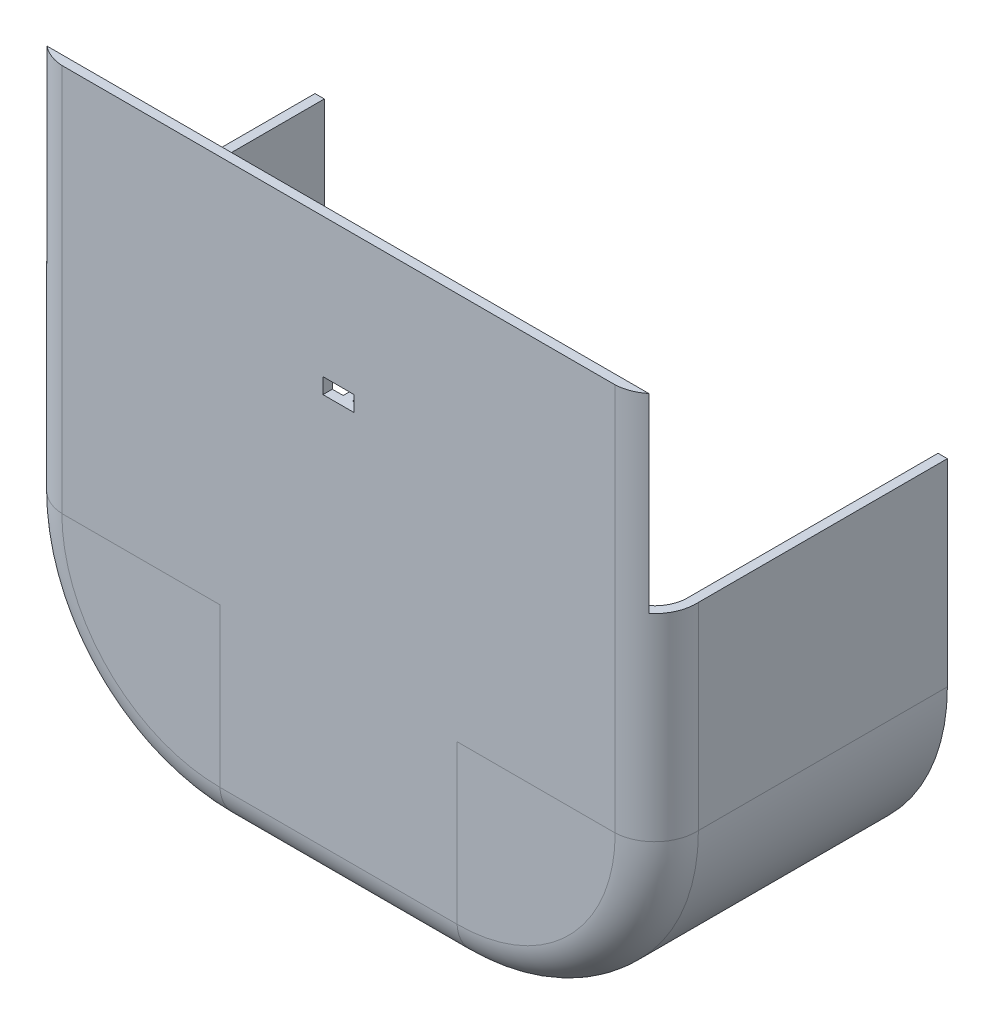
SolidWorks part; units mm, degrees
material "ABS"
ref_plane "Front Plane" through (0, 0, 0) normal (0, 0, 1) x (1, 0, 0)
ref_plane "Top Plane" through (0, 0, 0) normal (0, 1, 0) x (1, 0, 0)
ref_plane "Right Plane" through (0, 0, 0) normal (1, 0, 0) x (0, 0, -1)
sketch "Sketch1" plane through (0, 0, 0) normal (0, 0, 1) x (1, 0, 0)
  line L0 (-98.6, 98.6) -> (-98.6, -38.1)
  line L1 (-101.6, 101.6) -> (-101.6, -38.1)
  line L2 (-101.6, 101.6) -> (101.6, 101.6)
  line L3 (101.6, 101.6) -> (101.6, -38.1)
  line L4 (-38.1, -101.6) -> (38.1, -101.6)
  line L5 (-98.6, 98.6) -> (98.6, 98.6)
  line L6 (98.6, 98.6) -> (98.6, -38.1)
  line L7 (-38.1, -98.6) -> (38.1, -98.6)
  arc A0 (38.1, -101.6) -> (101.6, -38.1) centre (38.1, -38.1) ccw
  arc A1 (-101.6, -38.1) -> (-38.1, -101.6) centre (-38.1, -38.1) ccw
  arc A4 (98.6, -38.1) -> (38.1, -98.6) centre (38.1, -38.1) cw
  arc A5 (-38.1, -98.6) -> (-98.6, -38.1) centre (-38.1, -38.1) cw
  dimension "D5" = 63.5
  dimension "D6" = 63.5
  dimension "D1" = 203.2
  dimension "D2" = 139.7
  dimension "D3" = 139.7
  dimension "D4" = 76.2
  dimension "D7" = 101.6
  dimension "D8" = 101.6
  dimension "D9" = 3
  dimension "D10" = 3
  dimension "D11" = 3
  dimension "D12" = 3
  dimension "D13" = 0
  dimension "D14" = 0
  dimension "D15" = 0
  dimension "D16" = 0
extrude "Boss-Extrude1" add sketch "Sketch1" along normal blind 60 contours L1 A1 L4 A0 L3 L2 | L0 A5 L7 A4 L6 L5
sketch "Sketch3" plane through (0, 101.6, 0) normal (0, 1, 0) x (1, 0, 0)
  line L1 (-101.6, -60) -> (101.6, -60) construction
  line L2 (-38.1, -91.0391) -> (-88.9, -91.0391)
  line L3 (-98.6, -60) -> (-98.6, -80)
  line L4 (-38.1, -94.0391) -> (-38.1, -91.0391)
  line L7 (-98.6, -60) -> (-101.6, -60)
  line L9 (-101.6, -60) -> (-101.6, -80)
  line L10 (-38.1, -94.0391) -> (-88.9, -94.0391)
  arc A0 (-98.6, -80) -> (-88.9, -91.0391) centre (-88.0412, -80.5032) ccw
  arc A4 (-101.6, -80) -> (-88.9, -94.0391) centre (-88.2305, -80.6695) ccw
  dimension "D1" = 63.5
  dimension "D2" = 3
  dimension "D3" = 3
  dimension "D5" = 20
sketch "Sketch5" plane through (0, 0, 60) normal (0, 0, 1) x (1, 0, 0)
  line L0 (-100.1, 101.6) -> (-100.1, -38.1)
  line L1 (-98.6, 101.6) -> (-101.6, 101.6) construction
  line L2 (-101.6, 101.6) -> (-101.6, -38.1) construction
  line L3 (-38.1, -98.6) -> (-38.1, -101.6) construction
  line L4 (38.1, -98.6) -> (38.1, -101.6) construction
  line L5 (98.6, -38.1) -> (101.6, -38.1) construction
  line L6 (38.1, -100.1) -> (-38.1, -100.1)
  line L7 (100.1, -38.1) -> (100.1, 101.6)
  line L8 (-101.6, 101.6) -> (101.6, 101.6) construction
  arc A0 (-100.1, -38.1) -> (-38.1, -100.1) centre (-38.1, -38.1) ccw
  arc A1 (38.1, -100.1) -> (100.1, -38.1) centre (38.1, -38.1) ccw
  dimension "D1" = 0
  dimension "D2" = 1.5
  dimension "D3" = 0
sweep "Sweep2" add profiles "Sketch3" path "Sketch5"
sketch "Sketch6" plane through (0, 0, 94.0391) normal (0, 0, 1) x (1, 0, 0)
  line L0 (38.1, -38.1) -> (-38.1, -38.1)
  line L1 (-38.1, -38.1) -> (-38.1, 101.6)
  line L2 (-38.1, 101.6) -> (38.1, 101.6)
  line L3 (38.1, 101.6) -> (38.1, -38.1)
extrude "Boss-Extrude3" add sketch "Sketch6" against normal blind 3
sketch "Sketch7" plane through (0, 101.6, 0) normal (0, 1, 0) x (1, 0, 0)
  line L1 (122.4585, 44.29) -> (-132.2369, 44.29)
  line L2 (122.4585, 44.29) -> (122.4585, -91.0391)
  line L3 (122.4585, -91.0391) -> (-132.2369, -91.0391)
  line L4 (-132.2369, 44.29) -> (-132.2369, -91.0391)
  line L5 (122.4585, 44.29) -> (-132.2369, -91.0391) construction
  line L6 (122.4585, -91.0391) -> (-132.2369, 44.29) construction
  point P0 (-4.8892, -23.3746)
extrude "Cut-Extrude1" cut sketch "Sketch7" against normal blind 76.2
sketch "Sketch8" plane through (0, 0, 94.0391) normal (0, 0, 1) x (1, 0, 0)
  line L0 (0, 0) -> (0, 39.4405) construction
  line L2 (-5, 41.9405) -> (5, 41.9405)
  line L3 (-5, 41.9405) -> (-5, 36.9405)
  line L4 (-5, 36.9405) -> (5, 36.9405)
  line L5 (5, 41.9405) -> (5, 36.9405)
  line L6 (-5, 41.9405) -> (5, 36.9405) construction
  line L7 (-5, 36.9405) -> (5, 41.9405) construction
extrude "Cut-Extrude2" cut sketch "Sketch8" against normal through all
sketch "Sketch9" plane through (0, -101.6, 0) normal (0, -1, 0) x (-1, 0, 0)
  line L0 (38.1, 0) -> (-38.1, 0) construction
  line L1 (27.5, 0) -> (-27.5, 0)
  line L2 (27.5, 0) -> (27.5, -40)
  line L3 (27.5, -40) -> (-27.5, -40)
  line L4 (-27.5, 0) -> (-27.5, -40)
  line L5 (27.5, 0) -> (-27.5, -40) construction
  line L6 (27.5, -40) -> (-27.5, 0) construction
  line L7 (0, -20) -> (0, 0) construction
  point P0 (0, -20)
  dimension "D1" = 0
  dimension "D2" = 40
  dimension "D3" = 55
extrude "Cut-Extrude3" cut sketch "Sketch9" against normal through all
sketch "Sketch10" plane through (0, 101.6, 0) normal (0, 1, 0) x (1, 0, 0)
  line L0 (-88.9, -94.0391) -> (88.9, -94.0391) construction
  line L1 (100.3822, -101.2333) -> (-100.3822, -101.2333)
  line L2 (100.3822, -101.2333) -> (100.3822, -86.8449)
  line L3 (100.3822, -86.8449) -> (-100.3822, -86.8449)
  line L4 (-100.3822, -101.2333) -> (-100.3822, -86.8449)
  line L5 (100.3822, -101.2333) -> (-100.3822, -86.8449) construction
  line L6 (100.3822, -86.8449) -> (-100.3822, -101.2333) construction
  point P0 (0, -94.0391)
extrude "Cut-Extrude4" cut sketch "Sketch10" against normal blind 15
sketch "Sketch11" plane through (0, -98.6, 0) normal (0, 1, 0) x (1, 0, 0)
  line L0 (0, -40) -> (0, -80) construction
  line L1 (-27.5, -40) -> (27.5, -40) construction
  line L2 (-38.1, -80) -> (38.1, -80) construction
  line L3 (0, -80) -> (1.5, -80)
  line L4 (1.5, -80) -> (1.5, -40)
  line L5 (1.5, -40) -> (0, -40)
  line L6 (0, -80) -> (-1.5, -80)
  line L7 (-1.5, -80) -> (-1.5, -40)
  line L8 (-1.5, -40) -> (0, -40)
  dimension "D1" = 1.5
  dimension "D2" = 1.5
extrude "Boss-Extrude4" add sketch "Sketch11" along normal blind 4
sketch "Sketch12" plane through (0, 0, 91.0391) normal (0, 0, -1) x (-1, 0, 0)
  line L0 (0, -88.9) -> (0, 36.9405) construction
  line L1 (38.1, -88.9) -> (-38.1, -88.9) construction
  line L5 (-1.5, -88.9) -> (0, -88.9)
  line L6 (0, -88.9) -> (1.5, -88.9)
  line L7 (1.5, -88.9) -> (1.5, 36.9405)
  line L11 (-1.5, 36.9405) -> (1.5, 36.9405)
  line L12 (5, 36.9405) -> (-5, 36.9405) construction
  line L13 (-1.5, 36.9405) -> (-1.5, -88.9)
extrude "Boss-Extrude5" add sketch "Sketch12" along normal blind 4 contours L7 L11 L13 L5 L6
